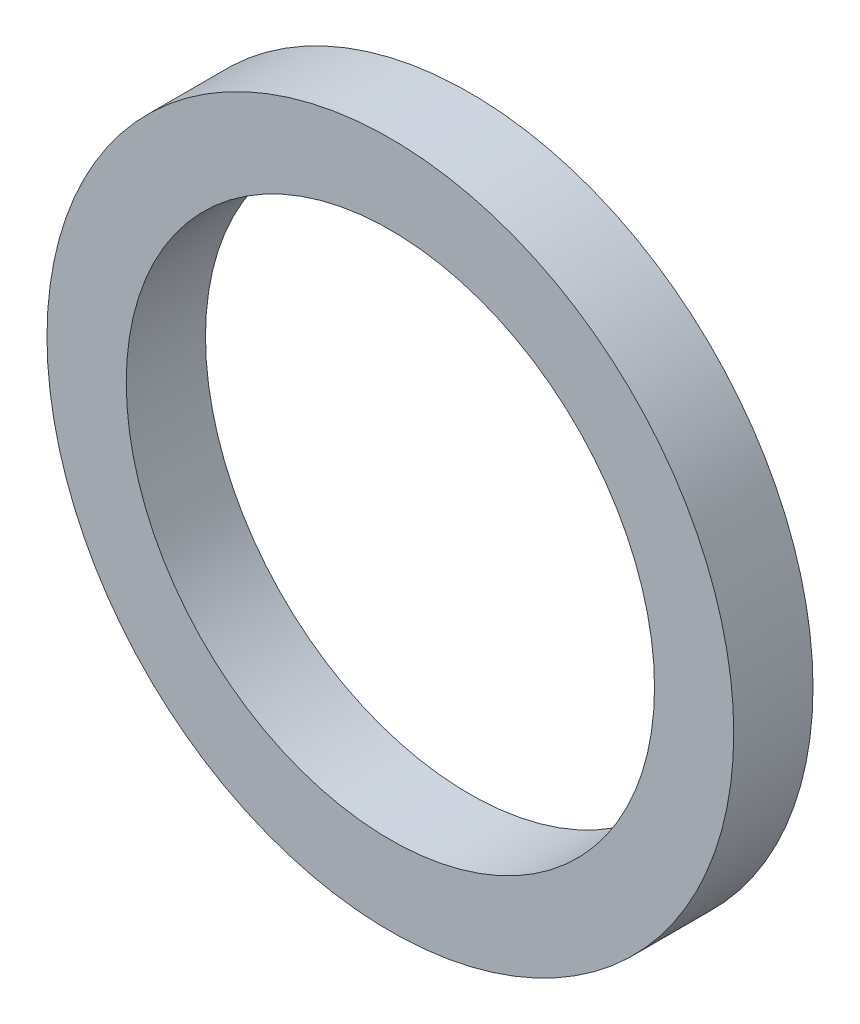
SolidWorks part; units mm, degrees
ref_plane "Front Plane" through (0, 0, 0) normal (0, 0, 1) x (1, 0, 0)
ref_plane "Top Plane" through (0, 0, 0) normal (0, 1, 0) x (1, 0, 0)
ref_plane "Right Plane" through (0, 0, 0) normal (1, 0, 0) x (0, 0, -1)
sketch "Sketch1" plane through (0, 0, 0) normal (0, 0, 1) x (1, 0, 0)
  circle A0 centre (0, 0) radius 13
  circle A2 centre (0, 0) radius 10
  dimension "D1" = 26
  dimension "D2" = 3
extrude "Boss-Extrude1" add sketch "Sketch1" along normal blind 3 contours A2
